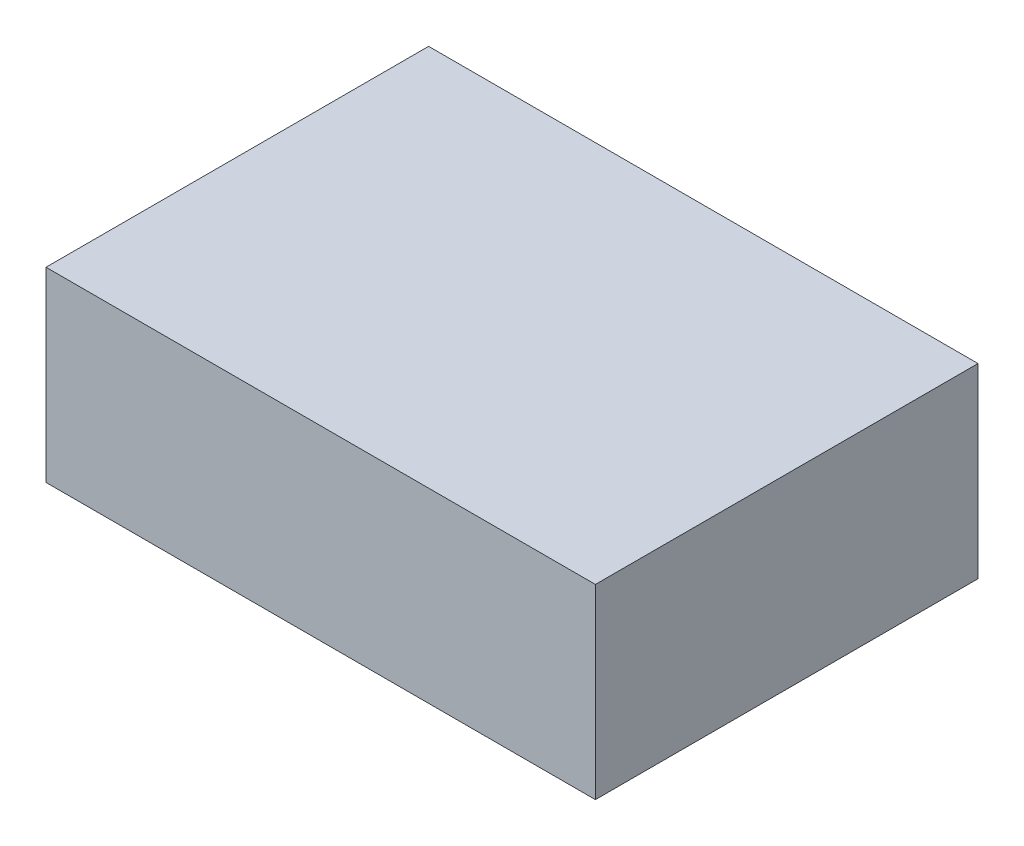
SolidWorks part; units mm, degrees
material "Nickel"
ref_plane "Front Plane" through (0, 0, 0) normal (0, 0, 1) x (1, 0, 0)
ref_plane "Top Plane" through (0, 0, 0) normal (0, 1, 0) x (1, 0, 0)
ref_plane "Right Plane" through (0, 0, 0) normal (1, 0, 0) x (0, 0, -1)
sketch "Sketch1" plane through (0, 0, 0) normal (0, 1, 0) x (1, 0, 0)
  line L1 (-56, 39) -> (56, 39)
  line L2 (-56, 39) -> (-56, -39)
  line L3 (-56, -39) -> (56, -39)
  line L4 (56, 39) -> (56, -39)
  line L5 (-56, 39) -> (56, -39) construction
  line L6 (-56, -39) -> (56, 39) construction
  point P0 (0, 0)
  dimension "D1" = 78
  dimension "D2" = 112
extrude "Boss-Extrude1" add sketch "Sketch1" along normal blind 38
